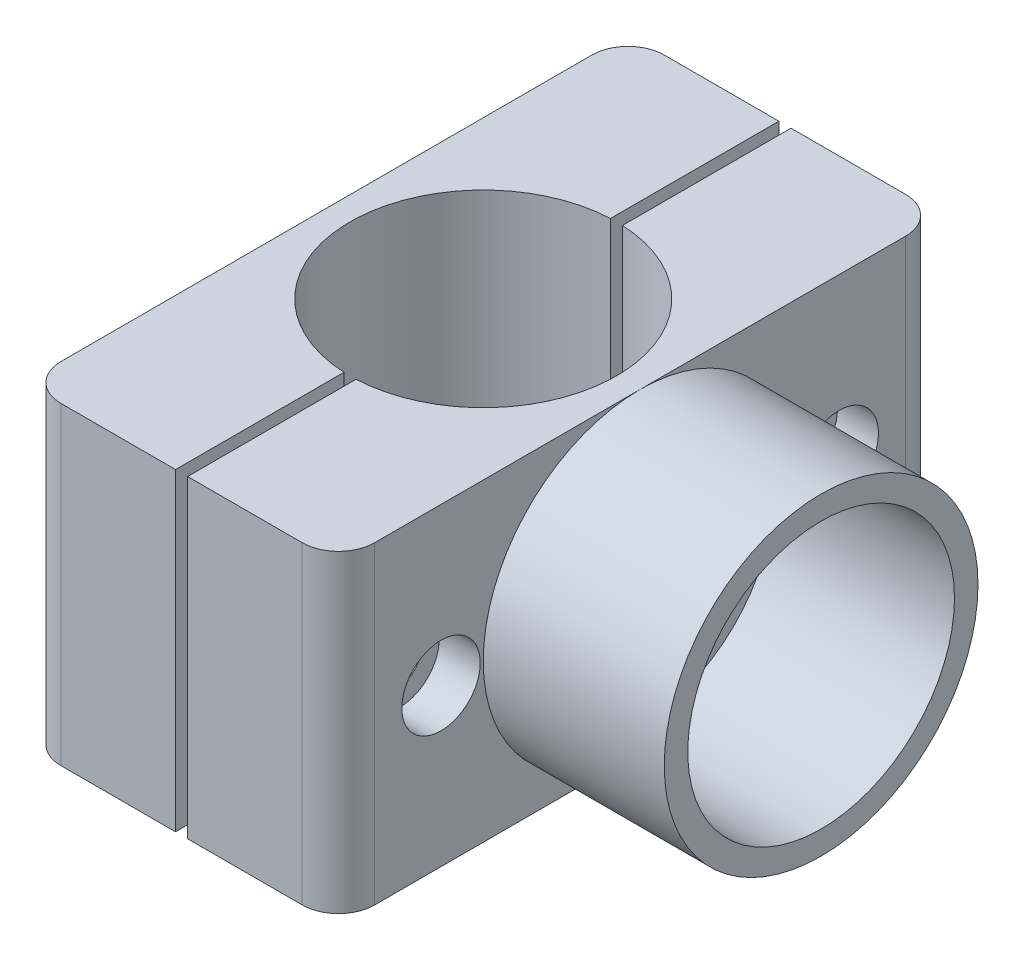
SolidWorks part; units mm, degrees
ref_plane "Front Plane" through (0, 0, 0) normal (0, 0, 1) x (1, 0, 0)
ref_plane "Top Plane" through (0, 0, 0) normal (0, 1, 0) x (1, 0, 0)
ref_plane "Right Plane" through (0, 0, 0) normal (1, 0, 0) x (0, 0, -1)
sketch "Croquis1" plane through (0, 0, 0) normal (0, 1, 0) x (1, 0, 0)
  line L0 (0, 25) -> (0, -25) construction
  line L1 (-13, -25) -> (13, -25)
  line L2 (-13, -25) -> (-13, 25)
  line L3 (-13, 25) -> (13, 25)
  line L5 (-13, -25) -> (0, 0) construction
  line L6 (-13, 25) -> (0, 0) construction
  line L9 (13, -25) -> (13, 25)
  circle A2 centre (0, 0) radius 11.05
  point P0 (0, 0)
  dimension "D1" = 22.1
  dimension "D2" = 50
  dimension "D3" = 13
extrude "Saliente-Extruir3" add sketch "Croquis1" along normal blind 26
sketch "Croquis22" plane through (0, 26, 0) normal (0, 1, 0) x (1, 0, 0)
  line L0 (0, 25) -> (0, -25) construction
  line L1 (-13, -25) -> (13, -25) construction
  line L2 (-13, -8) -> (13, -8) construction
  line L3 (13, -25) -> (13, 25) construction
  line L4 (13, -8) -> (13, -25) construction
  point P7 (0, 0)
  point P11 (0, -8)
sketch "Croquis23" plane through (13, 0, 0) normal (1, 0, 0) x (0, 0, -1)
  line L0 (-16.5, 26) -> (-16.5, 0) construction
  line L1 (-8, 26) -> (-25, 26) construction
  line L2 (-25, 0) -> (25, 0) construction
  line L3 (0, 55) -> (0, -55) construction
  line L4 (16.5, 26) -> (16.5, 0) construction
hole_wizard "Refrentado para tornillo con cabeza hueca de M31" positions "Croquis24" profile "Croquis25" counterbore size "M3" standard "DIN" end condition through all
sketch "Croquis24" plane through (13, 0, 0) normal (1, 0, 0) x (0, 0, -1)
  line L0 (-16.5, 26) -> (-16.5, 0) construction
  line L1 (16.5, 26) -> (16.5, 0) construction
  point P0 (-16.5, 13)
  point P4 (16.5, 13)
sketch "Croquis25" plane through (13, 13, 16.5) normal (0, 1, 0) x (0, 0, -1)
  line L0 (0, 0) -> (0, 26)
  line L1 (0, 26) -> (1.7, 26)
  line L3 (1.7, 26) -> (1.7, 3.4)
  line L4 (1.7, 3.4) -> (3.25, 3.4)
  line L5 (3.25, 3.4) -> (3.25, 0)
  line L7 (3.25, 0) -> (0, 0)
  line L11 (0, -6.35) -> (0, 107.95) construction
  dimension "Diámetro de taladro hasta el siguiente" = 3.4
  dimension "Profundidad de taladro hasta el siguiente" = 26
  dimension "Diámetro de refrentado" = 6.5
  dimension "Profundidad de refrentado" = 3.4
sketch "Croquis26" plane through (0, 0, 25) normal (0, 0, 1) x (1, 0, 0)
  line L0 (-13, 0) -> (13, 0) construction
  line L1 (-0.5, 0) -> (0.5, 0)
  line L2 (-0.5, 0) -> (-0.5, 26)
  line L3 (-0.5, 26) -> (0.5, 26)
  line L4 (0.5, 0) -> (0.5, 26)
  line L5 (-13, 26) -> (13, 26) construction
  point P8 (0, 0)
  dimension "D1" = 1
extrude "Cortar-Extruir2" cut sketch "Croquis26" against normal through all
sketch "Croquis27" plane through (-13, 0, 0) normal (-1, 0, 0) x (0, 0, 1)
  line L0 (-16.5, 26) -> (-16.5, 0) construction
  line L1 (-13.0359, 13) -> (-14.7679, 16)
  line L2 (-14.7679, 16) -> (-18.2321, 16)
  line L3 (-18.2321, 16) -> (-19.9641, 13)
  line L4 (-19.9641, 13) -> (-18.2321, 10)
  line L5 (-18.2321, 10) -> (-14.7679, 10)
  line L6 (-14.7679, 10) -> (-13.0359, 13)
  circle A0 centre (-16.5, 13) radius 3 construction
  dimension "D1" = 6
extrude "Cortar-Extruir3" cut sketch "Croquis27" against normal blind 3
mirror "Simetría8" about plane through (0, 0, 0) normal (0, 0, 1) of "Cortar-Extruir3"
sketch "Croquis28" plane through (13, 0, 0) normal (1, 0, 0) x (0, 0, -1)
  line L0 (-25, 13) -> (25, 13) construction
  line L1 (-25, 26) -> (-25, 0) construction
  line L2 (25, 26) -> (25, 0) construction
  line L3 (0, 26) -> (0, 0) construction
  circle A0 centre (0, 13) radius 13
  circle A1 centre (0, 13) radius 11.05
  point P14 (0, 13)
  dimension "D1" = 26
  dimension "D2" = 22.1
extrude "Saliente-Extruir4" add sketch "Croquis28" along normal blind 15
fillet "Redondeo1" radius 3 2 edges at (13, 13, -25) (13, 13, 25)
fillet "Redondeo2" radius 3 2 edges at (-13, 13, -25) (-13, 13, 25)
